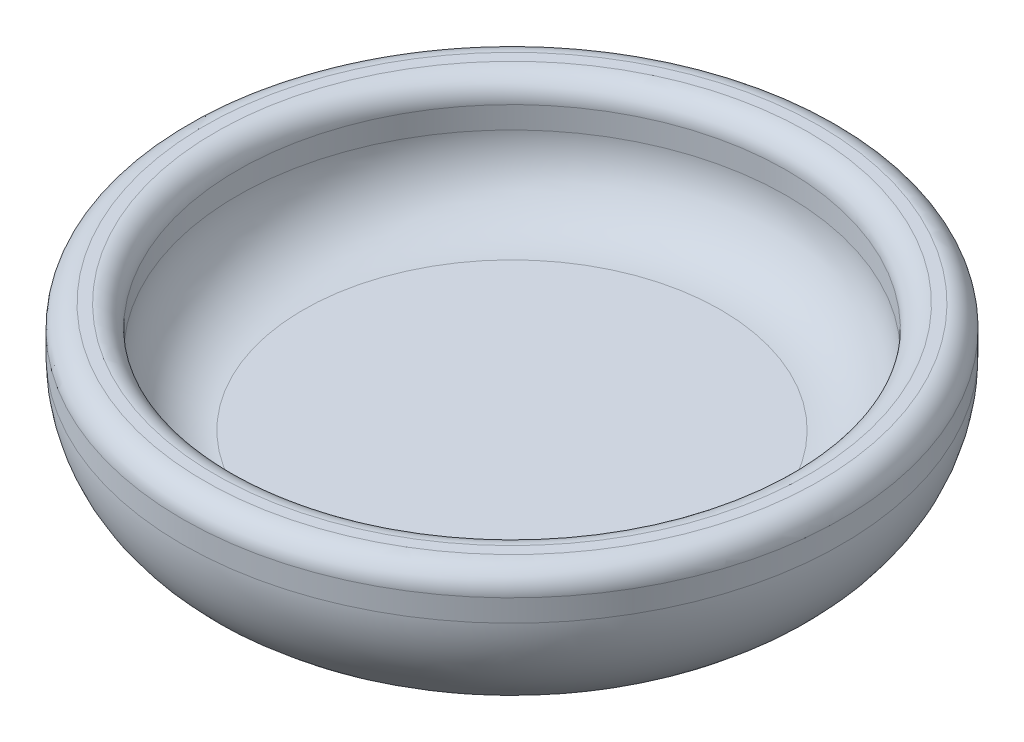
SolidWorks part; units mm, degrees
ref_plane "Front Plane" through (0, 0, 0) normal (0, 0, 1) x (1, 0, 0)
ref_plane "Top Plane" through (0, 0, 0) normal (0, 1, 0) x (1, 0, 0)
ref_plane "Right Plane" through (0, 0, 0) normal (1, 0, 0) x (0, 0, -1)
sketch "Sketch1" plane through (0, 0, 0) normal (0, 0, 1) x (1, 0, 0)
  line L0 (0, 0) -> (0, 6.35)
  line L1 (0, 6.35) -> (24.13, 6.35)
  line L2 (31.75, 13.97) -> (31.75, 16.51)
  line L3 (34.29, 19.05) -> (35.56, 19.05)
  line L4 (38.1, 16.51) -> (38.1, 13.97)
  line L5 (24.13, 0) -> (0, 0)
  arc A0 (24.13, 6.35) -> (31.75, 13.97) centre (24.13, 13.97) ccw
  arc A1 (35.56, 19.05) -> (38.1, 16.51) centre (35.56, 16.51) cw
  arc A2 (34.29, 19.05) -> (31.75, 16.51) centre (34.29, 16.51) ccw
  arc A3 (38.1, 13.97) -> (24.13, 0) centre (24.13, 13.97) cw
  point P11 (38.1, 19.05)
  point P14 (31.75, 19.05)
  point P17 (38.1, 0)
  dimension "D5" = 7.62
  dimension "D6" = 2.54
  dimension "D1" = 38.1
  dimension "D2" = 6.35
  dimension "D3" = 6.35
  dimension "D4" = 19.05
revolve "Revolve1" add sketch "Sketch1" angle 360 about L0
